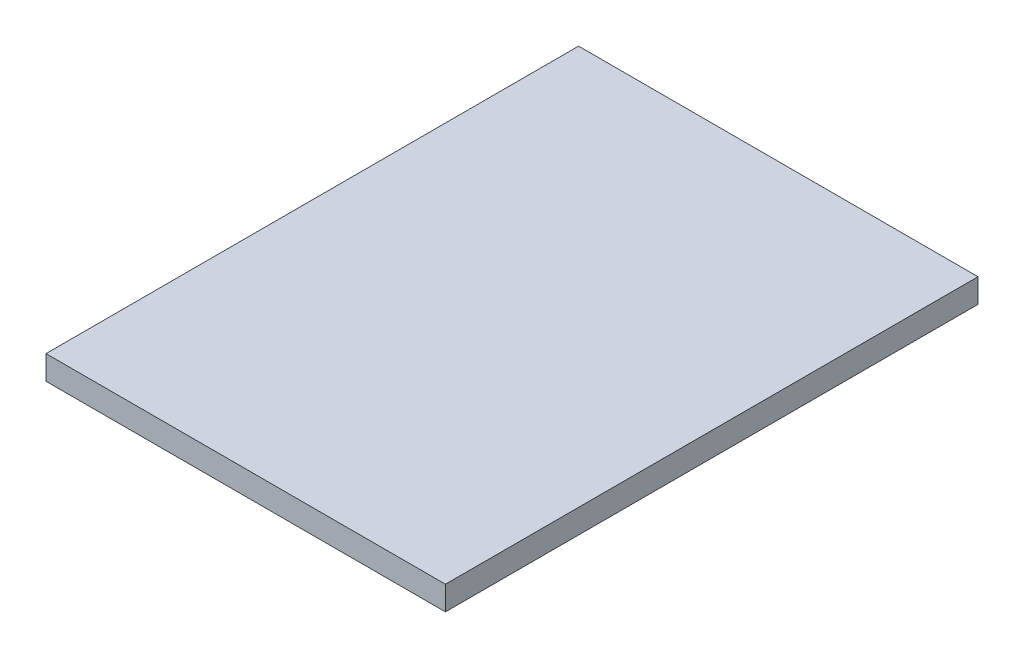
SolidWorks part; units mm, degrees
ref_plane "Front Plane" through (0, 0, 0) normal (0, 0, 1) x (1, 0, 0)
ref_plane "Top Plane" through (0, 0, 0) normal (0, 1, 0) x (1, 0, 0)
ref_plane "Right Plane" through (0, 0, 0) normal (1, 0, 0) x (0, 0, -1)
sketch "Sketch1" plane through (0, 0, 0) normal (0, 1, 0) x (1, 0, 0)
  line L1 (0, 0) -> (300, 0)
  line L2 (0, 0) -> (0, 400)
  line L3 (0, 400) -> (300, 400)
  line L4 (300, 0) -> (300, 400)
  dimension "D1" = 400
  dimension "D2" = 300
extrude "Boss-Extrude1" add sketch "Sketch1" along normal blind 18
